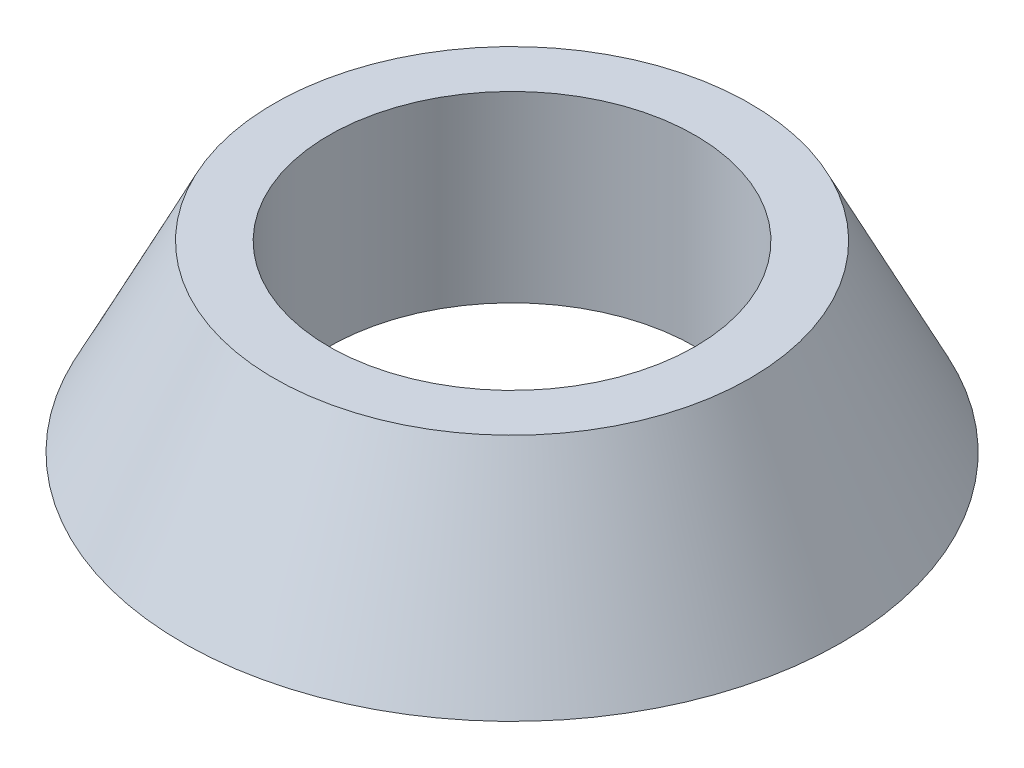
SolidWorks part; units mm, degrees
ref_plane "Płaszczyzna XY" through (0, 0, 0) normal (0, 0, 1) x (1, 0, 0)
ref_plane "Płaszczyzna XZ" through (0, 0, 0) normal (0, 1, 0) x (1, 0, 0)
ref_plane "Płaszczyzna YZ" through (0, 0, 0) normal (1, 0, 0) x (0, 0, -1)
sketch "Szkic1" plane through (0, 0, 0) normal (0, 0, 1) x (1, 0, 0)
  line L0 (0, 0) -> (0, 5.4167) construction
  line L1 (5, 0) -> (5, 5)
  line L3 (9, 0) -> (5, 0)
  line L4 (5, 5) -> (6.5, 5)
  line L5 (6.5, 5) -> (9, 0)
  dimension "D1" = 5
  dimension "D2" = 5
  dimension "D3" = 9
  dimension "D4" = 1.5
revolve "Obrót1" add sketch "Szkic1" angle 360 about L0
